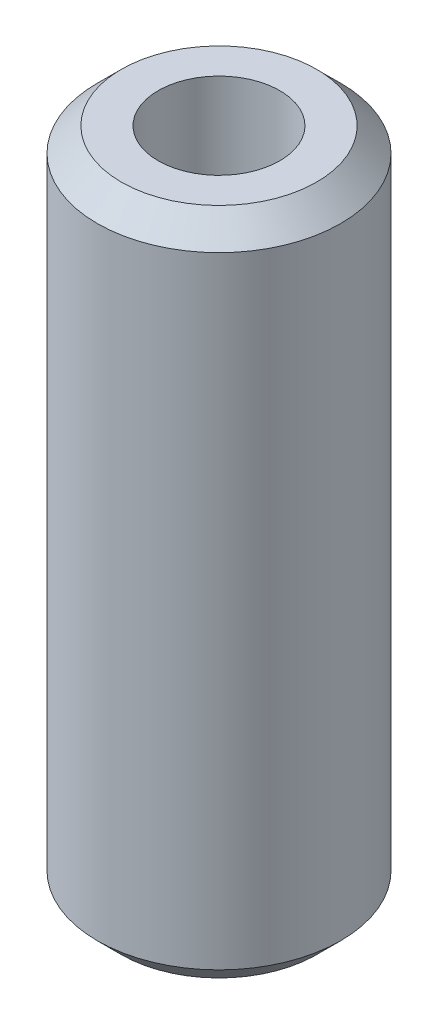
SolidWorks part; units mm, degrees
ref_plane "Front Plane" through (0, 0, 0) normal (0, 0, 1) x (1, 0, 0)
ref_plane "Top Plane" through (0, 0, 0) normal (0, 1, 0) x (1, 0, 0)
ref_plane "Right Plane" through (0, 0, 0) normal (1, 0, 0) x (0, 0, -1)
sketch "Schizzo1" plane through (0, 0, 0) normal (0, 1, 0) x (1, 0, 0)
  circle A0 centre (0, 0) radius 6.35
  circle A1 centre (0, 0) radius 12.7
  dimension "D1" = 12.7
  dimension "D2" = 25.4
extrude "Estrusione-Estrusione1" add sketch "Schizzo1" along normal mid plane 69.85
chamfer "Smusso1" distance 2.5 angle 45 2 edges at (0, -34.925, 12.7) (0, 34.925, 12.7)
